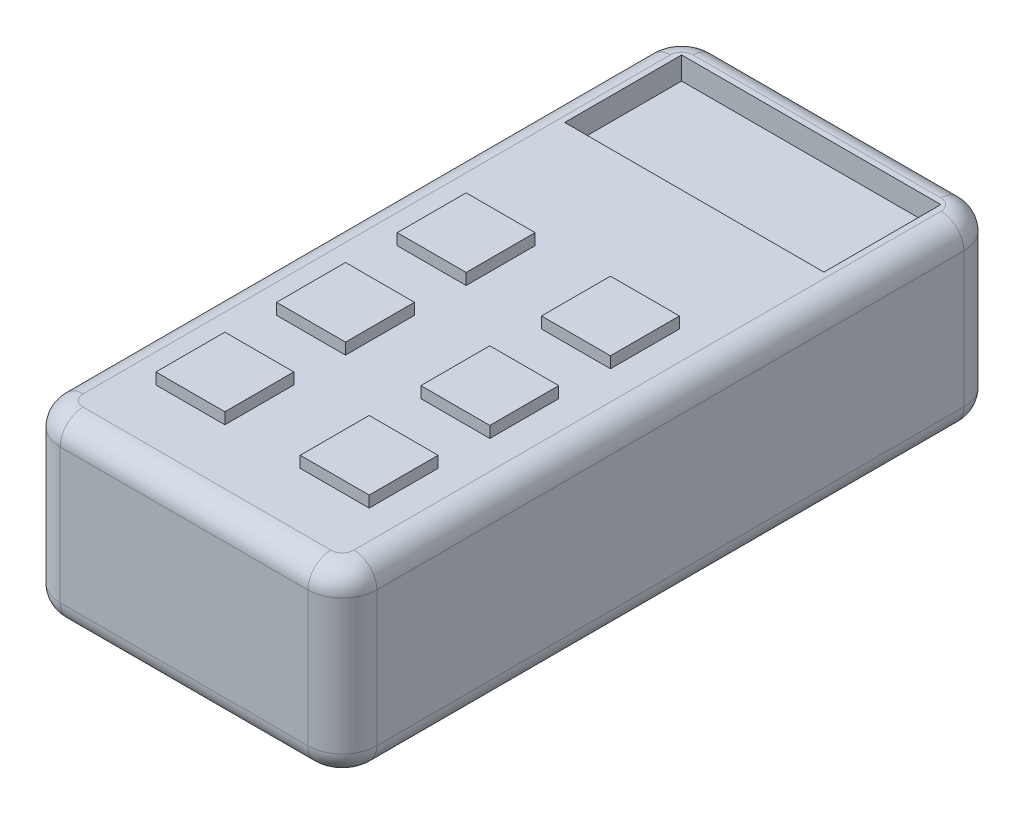
SolidWorks part; units mm, degrees
ref_plane "Front Plane" through (0, 0, 0) normal (0, 0, 1) x (1, 0, 0)
ref_plane "Top Plane" through (0, 0, 0) normal (0, 1, 0) x (1, 0, 0)
ref_plane "Right Plane" through (0, 0, 0) normal (1, 0, 0) x (0, 0, -1)
sketch "Sketch1" plane through (0, 0, 0) normal (0, 1, 0) x (1, 0, 0)
  line L1 (-35, -72.5) -> (35, -72.5)
  line L2 (-35, -72.5) -> (-35, 72.5)
  line L3 (-35, 72.5) -> (35, 72.5)
  line L4 (35, -72.5) -> (35, 72.5)
  line L5 (-35, -72.5) -> (35, 72.5) construction
  line L6 (-35, 72.5) -> (35, -72.5) construction
  point P0 (0, 0)
  dimension "D1" = 70
  dimension "D2" = 145
extrude "Boss-Extrude1" add sketch "Sketch1" along normal blind 40
sketch "Sketch2" plane through (0, 40, 0) normal (0, 1, 0) x (1, 0, 0)
  line L0 (-35, 72.5) -> (-35, -72.5) construction
  line L1 (-28.65, 66.15) -> (28.65, 66.15)
  line L2 (-28.65, 66.15) -> (-28.65, 40.3023)
  line L3 (-28.65, 40.3023) -> (28.65, 40.3023)
  line L4 (28.65, 66.15) -> (28.65, 40.3023)
  line L5 (35, -72.5) -> (35, 72.5) construction
  line L6 (35, 72.5) -> (-35, 72.5) construction
  dimension "D1" = 6.35
  dimension "D2" = 6.35
  dimension "D3" = 6.35
extrude "Cut-Extrude1" cut sketch "Sketch2" against normal blind 5
sketch "Sketch3" plane through (0, 40, 0) normal (0, 1, 0) x (1, 0, 0)
  line L0 (-35, 72.5) -> (-35, -72.5) construction
  line L1 (-23.57, 13.4341) -> (-8.33, 13.4341)
  line L2 (-23.57, 13.4341) -> (-23.57, -1.8059)
  line L3 (-23.57, -1.8059) -> (-8.33, -1.8059)
  line L4 (-8.33, 13.4341) -> (-8.33, -1.8059)
  line L5 (35, -72.5) -> (35, 72.5) construction
  line L6 (8.33, 13.4341) -> (23.57, 13.4341)
  line L7 (8.33, 13.4341) -> (8.33, -1.8059)
  line L8 (8.33, -1.8059) -> (23.57, -1.8059)
  line L9 (23.57, 13.4341) -> (23.57, -1.8059)
  dimension "D1" = 15.24
  dimension "D2" = 15.24
  dimension "D3" = 11.43
  dimension "D4" = 15.24
  dimension "D5" = 15.24
  dimension "D6" = 11.43
extrude "Boss-Extrude2" add sketch "Sketch3" along normal blind 2.5
pattern_linear "LPattern1" count 3 spacing 26.67 along (0, 0, 1) of "Boss-Extrude2"
fillet "Fillet1" radius 7.62 4 edges at (35, 20, 72.5) (-35, 20, 72.5) (-35, 20, -72.5) (35, 20, -72.5)
fillet "Fillet2" radius 5.08 8 edges at (-32.7682, 40, 70.2682) (-35, 40, 0) (-32.7682, 40, -70.2682) (0, 40, -72.5) (32.7682, 40, -70.2682) (35, 40, 0) (32.7682, 40, 70.2682) (0, 40, 72.5)
fillet "Fillet3" radius 5.08 8 edges at (32.7682, 0, 70.2682) (0, 0, 72.5) (-32.7682, 0, 70.2682) (-35, 0, 0) (-32.7682, 0, -70.2682) (0, 0, -72.5) (32.7682, 0, -70.2682) (35, 0, 0)
